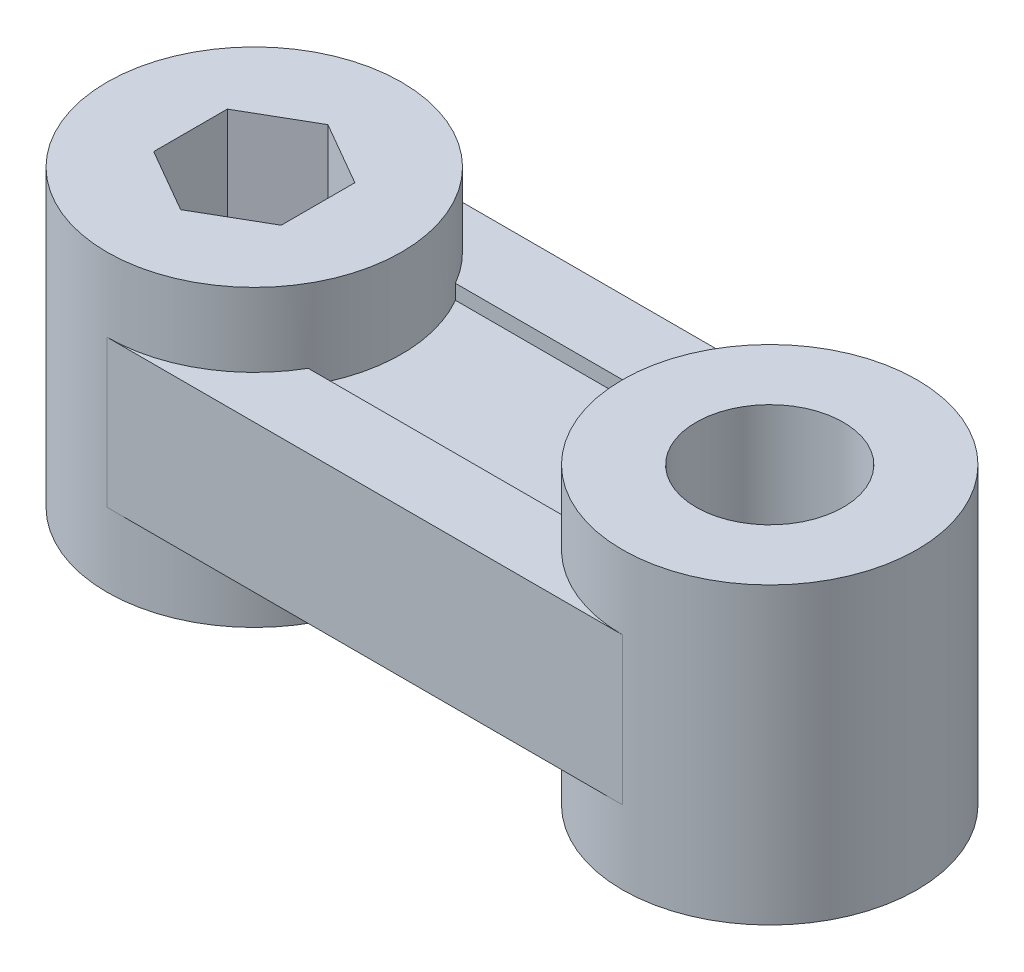
SolidWorks part; units mm, degrees
ref_plane "Front Plane" through (0, 0, 0) normal (0, 0, 1) x (1, 0, 0)
ref_plane "Top Plane" through (0, 0, 0) normal (0, 1, 0) x (1, 0, 0)
ref_plane "Right Plane" through (0, 0, 0) normal (1, 0, 0) x (0, 0, -1)
sketch "Sketch1" plane through (0, 0, 0) normal (0, 1, 0) x (1, 0, 0)
  line L0 (0, 0) -> (35, 0) construction
  line L1 (0, 10) -> (35, 10)
  line L2 (0, 5) -> (-4.3301, 2.5)
  line L3 (-4.3301, 2.5) -> (-4.3301, -2.5)
  line L4 (-4.3301, -2.5) -> (0, -5)
  line L5 (0, -5) -> (4.3301, -2.5)
  line L6 (4.3301, -2.5) -> (4.3301, 2.5)
  line L7 (4.3301, 2.5) -> (0, 5)
  line L8 (0, -10) -> (35, -10)
  arc A0 (0, 10) -> (0, -10) centre (0, 0) ccw
  arc A1 (35, -10) -> (35, 10) centre (35, 0) ccw
  circle A2 centre (0, 0) radius 4.3301 construction
  circle A3 centre (35, 0) radius 5
  dimension "D2" = 20
  dimension "D1" = 35
  dimension "D3" = 10
extrude "Boss-Extrude1" add sketch "Sketch1" along normal blind 20
sketch "Sketch2" plane through (0, 20, 0) normal (0, 1, 0) x (1, 0, 0)
  line L0 (0, 10) -> (35, 10)
  line L2 (35, -10) -> (0, -10)
  arc A0 (0, -10) -> (0, 10) centre (0, 0) ccw
  arc A1 (35, 10) -> (35, -10) centre (35, 0) ccw
extrude "Cut-Extrude2" cut sketch "Sketch2" against normal blind 5
sketch "Sketch3" plane through (0, 15, 0) normal (0, 1, 0) x (1, 0, 0)
  line L0 (25, 0) -> (10, 0) construction
  line L1 (26.3397, 5) -> (8.6603, 5)
  line L3 (8.6603, -5) -> (26.3397, -5)
  arc A0 (8.6603, -5) -> (8.6603, 5) centre (0, 0) ccw
  arc A1 (26.3397, 5) -> (26.3397, -5) centre (35, 0) ccw
extrude "Cut-Extrude3" cut sketch "Sketch3" against normal blind 1
sketch "Sketch4" plane through (0, 0, 0) normal (0, -1, 0) x (1, 0, 0)
  line L2 (0, -10) -> (35, -10)
  line L3 (35, 10) -> (0, 10)
  line L4 (0, -10) -> (35, -10)
  line L5 (35, 10) -> (0, 10)
  line L6 (8.6603, 5) -> (26.3397, 5)
  line L7 (35, 10) -> (0, 10)
  line L9 (35, 10) -> (0, 10)
  line L11 (35, -10) -> (0, -10) construction
  line L13 (0, 10) -> (35, 10) construction
  line L17 (35, -10) -> (0, -10)
  line L19 (0, 10) -> (35, 10)
  arc A0 (26.3397, 5) -> (26.3397, -5) centre (35, 0) ccw construction
  arc A1 (8.6603, -5) -> (8.6603, 5) centre (0, 0) ccw construction
  arc A2 (0, 10) -> (0, -10) centre (0, 0) ccw
  arc A3 (35, -10) -> (35, 10) centre (35, 0) ccw
  arc A6 (8.6603, 5) -> (0, 10) centre (0, 0) ccw
  arc A7 (35, 10) -> (26.3397, 5) centre (35, 0) ccw
  arc A8 (8.6603, 5) -> (0, 10) centre (0, 0) ccw
  arc A9 (35, 10) -> (26.3397, 5) centre (35, 0) ccw
  arc A10 (26.3397, -5) -> (35, -10) centre (35, 0) ccw construction
  arc A11 (0, -10) -> (8.6603, -5) centre (0, 0) ccw construction
  arc A12 (8.6603, 5) -> (0, 10) centre (0, 0) ccw construction
  arc A13 (35, 10) -> (26.3397, 5) centre (35, 0) ccw construction
  arc A14 (26.3397, 5) -> (26.3397, -5) centre (35, 0) ccw
  arc A15 (8.6603, -5) -> (8.6603, 5) centre (0, 0) ccw
  arc A16 (26.3397, -5) -> (35, -10) centre (35, 0) ccw
  arc A17 (0, -10) -> (8.6603, -5) centre (0, 0) ccw
  arc A18 (8.6603, 5) -> (0, 10) centre (0, 0) ccw
  arc A19 (35, 10) -> (26.3397, 5) centre (35, 0) ccw
  line M11 (0, -10) -> (35, -10)
  line M13 (35, 10) -> (0, 10)
  dimension "D1" = 0
  dimension "D2" = 0
extrude "Cut-Extrude4" cut sketch "Sketch4" against normal blind 5 contours A17 A16 A14 A9 A8 A15 M11 M13
sketch "Sketch5" plane through (0, 5, 0) normal (0, -1, 0) x (1, 0, 0)
  line L2 (0, -10) -> (35, -10)
  line L3 (35, 10) -> (0, 10)
  line L4 (0, -10) -> (35, -10)
  line L5 (35, 10) -> (0, 10)
  line L6 (8.6603, -5) -> (26.3397, -5)
  line L7 (26.3397, 5) -> (8.6603, 5)
  line L8 (8.6603, -5) -> (26.3397, -5)
  line L9 (26.3397, 5) -> (8.6603, 5)
  arc A2 (0, -10) -> (0, 10) centre (0, 0) ccw
  arc A3 (35, 10) -> (35, -10) centre (35, 0) ccw
  arc A4 (0, -10) -> (0, 10) centre (0, 0) ccw
  arc A5 (35, 10) -> (35, -10) centre (35, 0) ccw
  arc A6 (26.3397, 5) -> (26.3397, -5) centre (35, 0) ccw
  arc A7 (8.6603, -5) -> (8.6603, 5) centre (0, 0) ccw
  arc A8 (26.3397, 5) -> (26.3397, -5) centre (35, 0) ccw
  arc A9 (8.6603, -5) -> (8.6603, 5) centre (0, 0) ccw
  arc M9 (0, 10) -> (0, -10) centre (0, 0) cw
  arc M11 (35, -10) -> (35, 10) centre (35, 0) cw
  dimension "D1" = 0
  dimension "D2" = 0
extrude "Cut-Extrude5" cut sketch "Sketch5" against normal blind 1 contours L9 L8 M11 M9
